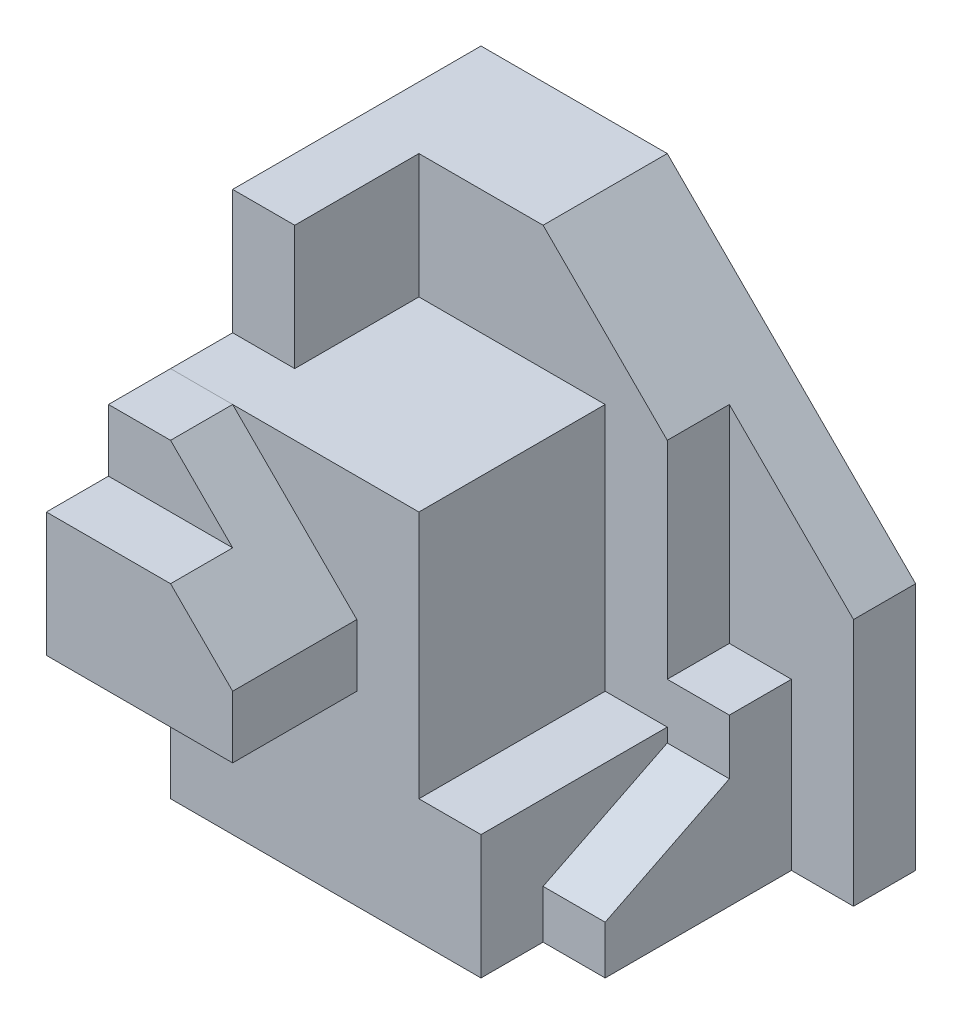
SolidWorks part; units mm, degrees
ref_plane "Front Plane" through (0, 0, 0) normal (0, 0, 1) x (1, 0, 0)
ref_plane "Top Plane" through (0, 0, 0) normal (0, 1, 0) x (1, 0, 0)
ref_plane "Right Plane" through (0, 0, 0) normal (1, 0, 0) x (0, 0, -1)
sketch "Sketch1" plane through (0, 0, 0) normal (0, 1, 0) x (1, 0, 0)
  line L1 (-25, -25) -> (25, -25)
  line L2 (-25, -25) -> (-25, 25)
  line L3 (-25, 25) -> (25, 25)
  line L4 (25, -25) -> (25, 25)
  line L5 (-25, -25) -> (25, 25) construction
  line L6 (-25, 25) -> (25, -25) construction
  point P0 (0, 0)
  dimension "D1" = 50
  dimension "D2" = 50
extrude "Boss-Extrude1" add sketch "Sketch1" along normal blind 60
sketch "Sketch2" plane through (0, 60, 0) normal (0, 1, 0) x (1, 0, 0)
  line L1 (25, -25) -> (15, -25)
  line L2 (25, -25) -> (25, 5)
  line L3 (25, 5) -> (15, 5)
  line L4 (15, -25) -> (15, 5)
  dimension "D1" = 30
  dimension "D2" = 10
extrude "Cut-Extrude1" cut sketch "Sketch2" against normal blind 40
sketch "Sketch3" plane through (0, 60, 0) normal (0, 1, 0) x (1, 0, 0)
  line L1 (-25, -25) -> (5, -25)
  line L2 (-25, -25) -> (-25, -45)
  line L3 (-25, -45) -> (5, -45)
  line L4 (5, -25) -> (5, -45)
  dimension "D1" = 30
  dimension "D2" = 20
extrude "Boss-Extrude2" add sketch "Sketch3" against normal blind 30 separate body
chamfer "Chamfer1" distance 20 distance2 20 1 edges at (5, 60, 35)
sketch "Sketch4" plane through (-25, 0, 0) normal (-1, 0, 0) x (0, 0, 1)
  line L1 (45, 60) -> (35, 60)
  line L2 (45, 60) -> (45, 50)
  line L3 (45, 50) -> (35, 50)
  line L4 (35, 60) -> (35, 50)
  dimension "D1" = 10
  dimension "D2" = 10
extrude "Cut-Extrude2" cut sketch "Sketch4" against normal blind 40
sketch "Sketch6" plane through (25, 0, 0) normal (1, 0, 0) x (0, 0, -1)
  line L0 (-25, 0) -> (25, 0) construction
  line L1 (25, 0) -> (15, 0)
  line L2 (25, 0) -> (25, 80)
  line L3 (25, 80) -> (15, 80)
  line L4 (15, 0) -> (15, 80)
  line L5 (25, 60) -> (25, 0) construction
  dimension "D1" = 80
  dimension "D2" = 10
extrude "Boss-Extrude3" add sketch "Sketch6" along normal blind 20
sketch "Sketch7" plane through (0, 60, 0) normal (0, 1, 0) x (1, 0, 0)
  line L0 (-25, -15) -> (-15, -15)
  line L2 (-15, -15) -> (-15, 5)
  line L3 (-15, 5) -> (25, 5)
  line L4 (25, 5) -> (25, 15) construction
  line L5 (25, 5) -> (25, 15)
  line L6 (25, 15) -> (25, 25)
  line L7 (25, 25) -> (-25, 25)
  line L8 (-25, 25) -> (-25, -25) construction
  line L9 (-25, -15) -> (-25, 25)
  dimension "D1" = 40
  dimension "D2" = 10
  dimension "D3" = 20
  dimension "D4" = 20
extrude "Boss-Extrude4" add sketch "Sketch7" along normal blind 20
chamfer "Chamfer2" distance 40 distance2 40 1 edges at (45, 80, -20)
sketch "Sketch8" plane through (25, 0, 0) normal (1, 0, 0) x (0, 0, -1)
  line L0 (15, 26.6693) -> (15, 0)
  line L1 (15, 60) -> (15, 0) construction
  line L2 (15, 40) -> (15, 0) construction
  line L3 (15, 0) -> (-15, 0)
  line L4 (-25, 0) -> (15, 0) construction
  line L5 (-15, 0) -> (-15, 7.7822)
  line L6 (-15, 7.7822) -> (5, 17.7822)
  line L7 (5, 17.7822) -> (5, 26.6693)
  line L8 (5, 26.6693) -> (15, 26.6693)
  dimension "D1" = 10
  dimension "D2" = 10
  dimension "D3" = 20
extrude "Boss-Extrude5" add sketch "Sketch8" along normal blind 10
